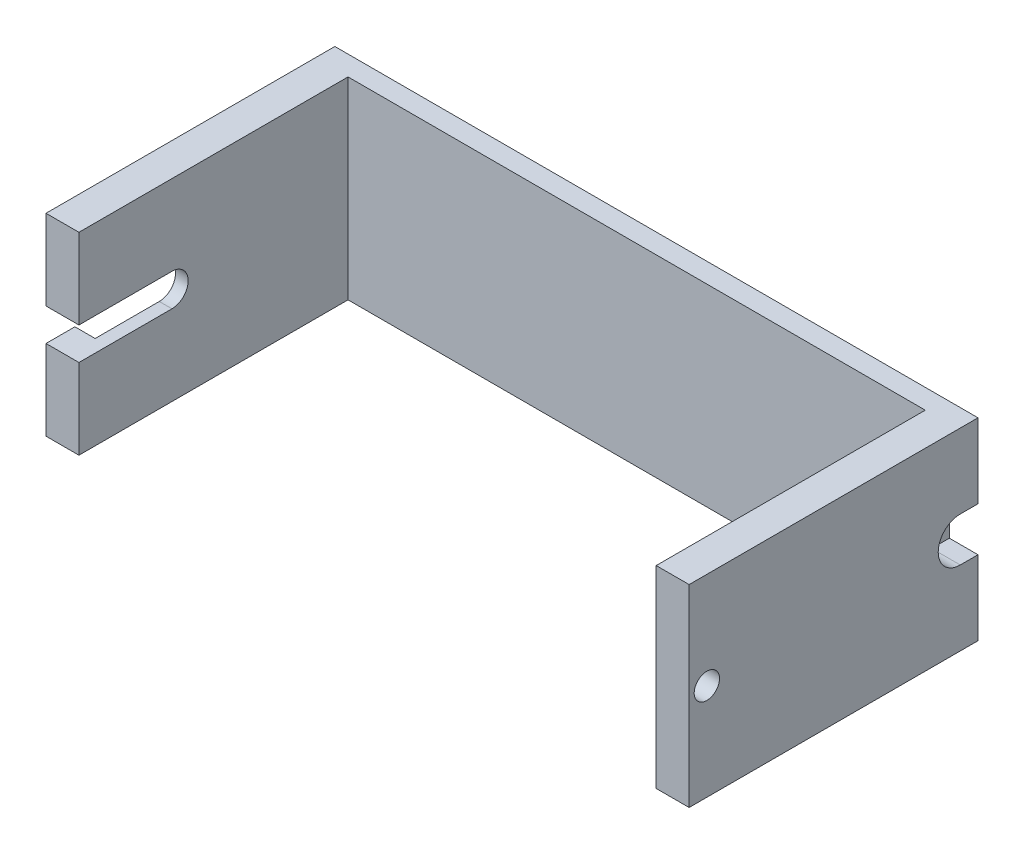
SolidWorks part; units mm, degrees
ref_plane "Plano frontal" through (0, 0, 0) normal (0, 0, 1) x (1, 0, 0)
ref_plane "Plano superior" through (0, 0, 0) normal (0, 1, 0) x (1, 0, 0)
ref_plane "Plano direito" through (0, 0, 0) normal (1, 0, 0) x (0, 0, -1)
sketch "Esboço1" plane through (0, 0, 0) normal (0, 0, 1) x (1, 0, 0)
  line L1 (0, 0) -> (-126.9, 0)
  line L2 (0, 0) -> (0, 38.1)
  line L3 (0, 38.1) -> (-126.9, 38.1)
  line L4 (-126.9, 0) -> (-126.9, 38.1)
  dimension "D1" = 126.9
  dimension "D2" = 38.1
extrude "Ressalto-extrusão2" add sketch "Esboço1" along normal blind 3.9
sketch "Esboço3" plane through (0, 0, 3.9) normal (0, 0, 1) x (1, 0, 0)
  line L0 (-126.9, 0) -> (0, 0) construction
  line L1 (-126.9, 38.1) -> (-120.4, 38.1)
  line L2 (-126.9, 38.1) -> (-126.9, 0)
  line L3 (-126.9, 0) -> (-120.4, 0)
  line L4 (-120.4, 38.1) -> (-120.4, 0)
  line L6 (0, 38.1) -> (-6.5, 38.1)
  line L7 (0, 38.1) -> (0, 0)
  line L8 (0, 0) -> (-6.5, 0)
  line L9 (-6.5, 38.1) -> (-6.5, 0)
extrude "Ressalto-extrusão3" add sketch "Esboço3" along normal blind 53.1
sketch "Esboço4" plane through (-126.9, 0, 0) normal (-1, 0, 0) x (0, 0, 1)
  line L0 (57, 19.05) -> (0, 19.05) construction
  line L1 (57, 38.1) -> (57, 0) construction
  line L2 (0, 38.1) -> (0, 0) construction
  line L3 (28.5, 0) -> (28.5, 6.4) construction
  line L5 (57, 0) -> (0, 0) construction
  line L6 (28.5, 38.1) -> (28.5, 31.7) construction
  line L7 (57, 38.1) -> (0, 38.1) construction
  line L8 (57, 19.05) -> (51.3, 19.05) construction
  line L10 (51.3, 31.7) -> (26, 31.7)
  line L11 (51.3, 31.7) -> (51.3, 6.4)
  line L12 (51.3, 6.4) -> (26, 6.4)
  line L13 (26, 31.7) -> (26, 6.4)
  circle A0 centre (38.65, 19.05) radius 3.2
  point P19 (38.65, 19.05)
extrude "Corte-extrusão1" cut sketch "Esboço4" against normal blind 4
sketch "Esboço6" plane through (-126.9, 0, 0) normal (-1, 0, 0) x (0, 0, 1)
  line L0 (38.65, 22.25) -> (57, 22.25)
  line L1 (57, 38.1) -> (57, 0) construction
  line L2 (57, 22.25) -> (57, 15.85)
  line L3 (57, 15.85) -> (38.65, 15.85)
  arc A0 (38.65, 22.25) -> (38.65, 15.85) centre (38.65, 19.05) ccw
extrude "Corte-extrusão2" cut sketch "Esboço6" against normal blind 50
sketch "Esboço7" plane through (0, 0, 0) normal (1, 0, 0) x (0, 0, -1)
  line L2 (0, 19.05) -> (-3.5, 19.05) construction
  line L3 (0, 0) -> (0, 38.1) construction
  line L4 (-3.5, 14.7) -> (0, 14.7)
  line L5 (0, 14.7) -> (0, 23.4)
  line L6 (0, 23.4) -> (-3.5, 23.4)
  arc A0 (-3.5, 23.4) -> (-3.5, 14.7) centre (-3.5, 19.05) ccw
extrude "Corte-extrusão3" cut sketch "Esboço7" against normal blind 5.65
sketch "Esboço9" plane through (0, 0, 0) normal (1, 0, 0) x (0, 0, -1)
  line L0 (0, 23.4) -> (0, 14.7) construction
  line L1 (0, 19.05) -> (-32.3369, 19.05) construction
  line L2 (-57, 19.05) -> (-53.5, 19.05) construction
  circle A0 centre (-53.5, 19.05) radius 2.5
extrude "Corte-extrusão4" cut sketch "Esboço9" against normal blind 10
